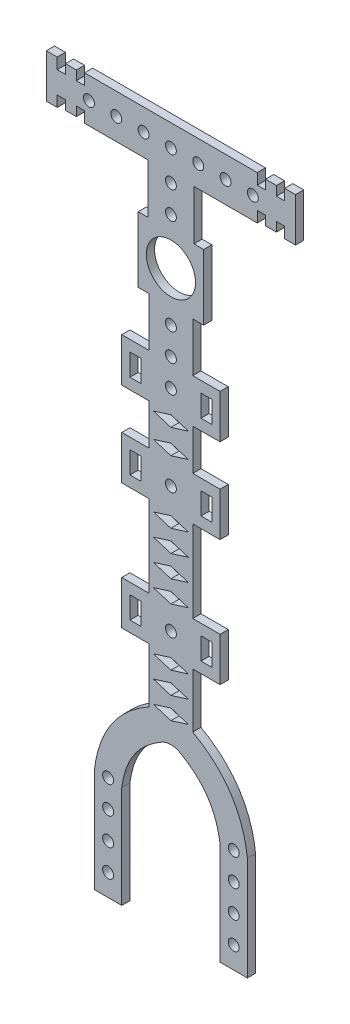
SolidWorks part; units mm, degrees
ref_plane "前视基准面" through (0, 0, 0) normal (0, 0, 1) x (1, 0, 0)
ref_plane "上视基准面" through (0, 0, 0) normal (0, 1, 0) x (1, 0, 0)
ref_plane "右视基准面" through (0, 0, 0) normal (1, 0, 0) x (0, 0, -1)
other "Configuration Table"
sketch "草图1" plane through (0, 0, 0) normal (0, 0, 1) x (1, 0, 0)
  line L0 (0, 13.5) -> (0, 5.7352) construction
  line L1 (0, 0) -> (8.7713, 0) construction
  line L2 (-4.2111, 7) -> (-4.2111, 16.1056)
  line L3 (-6, 7) -> (6, 7)
  line L4 (-6, 7) -> (-6, -5)
  line L5 (-6, -5) -> (6, -5)
  line L6 (6, 7) -> (6, -5)
  line L7 (-6, 7) -> (6, -5) construction
  line L8 (-6, -5) -> (6, 7) construction
  line L9 (-4.2111, 16.1056) -> (-15.8161, 16.1056)
  line L10 (-19.3161, 16.4056) -> (-19.3161, 18.1056)
  line L11 (-20.8161, 24.1056) -> (-22.8161, 24.1056)
  line L12 (20.8161, 16.1056) -> (22.8161, 16.1056)
  line L13 (19.3161, 18.1056) -> (20.8161, 18.1056)
  line L14 (4.2111, 16.1056) -> (4.2111, 7)
  line L15 (-22.8161, 24.1056) -> (-22.8161, 16.1056)
  line L16 (-19.3161, 22.1056) -> (-20.8161, 22.1056)
  line L17 (-20.8161, 22.1056) -> (-20.8161, 24.1056)
  line L18 (-17.3161, 16.4056) -> (-19.3161, 16.4056)
  line L19 (-17.3161, 18.1056) -> (-17.3161, 16.4056)
  line L20 (-15.8161, 18.1056) -> (-17.3161, 18.1056)
  line L21 (20.8161, 18.1056) -> (20.8161, 16.1056)
  line L22 (19.3161, 23.8056) -> (19.3161, 22.1056)
  line L23 (17.3161, 23.8056) -> (19.3161, 23.8056)
  line L24 (17.3161, 22.1056) -> (17.3161, 23.8056)
  line L25 (15.8161, 22.1056) -> (17.3161, 22.1056)
  line L26 (15.8161, 24.1056) -> (15.8161, 22.1056)
  line L27 (-15.8161, 24.1056) -> (15.8161, 24.1056)
  line L28 (-15.8161, 16.1056) -> (-15.8161, 18.1056)
  line L29 (15.8161, 16.1056) -> (15.8161, 18.1056)
  line L30 (15.8161, 16.1056) -> (4.2111, 16.1056)
  line L31 (-25.1648, 20.1056) -> (-15.2017, 20.1056) construction
  line L32 (0, 20.1056) -> (5, 20.1056) construction
  line L33 (0, 20.1056) -> (-5, 20.1056) construction
  line L34 (-4, -14) -> (-4, -5)
  line L35 (-4, -14) -> (-9, -14)
  line L36 (-9, -14) -> (-9, -22)
  line L37 (-9, -22) -> (-4, -22)
  line L38 (-4, -22) -> (-4, -29.5)
  line L39 (-4, -29.5) -> (-9, -29.5)
  line L40 (-9, -29.5) -> (-9, -37.5)
  line L41 (-9, -37.5) -> (-4, -37.5)
  line L42 (-7.5, -31.5) -> (-5.5, -31.5)
  line L43 (-4, -52.5) -> (-9, -52.5)
  line L44 (-9, -52.5) -> (-9, -60.5)
  line L45 (-9, -60.5) -> (-4, -60.5)
  line L46 (-4, -60.5) -> (-4, -70.5)
  line L47 (15.8161, 18.1056) -> (17.3161, 18.1056)
  line L48 (4, -70.5) -> (4, -60.5)
  line L49 (4, -60.5) -> (9, -60.5)
  line L50 (9, -60.5) -> (9, -52.5)
  line L51 (9, -52.5) -> (4, -52.5)
  line L52 (4, -52.5) -> (4, -37.5)
  line L53 (4, -37.5) -> (9, -37.5)
  line L54 (9, -37.5) -> (9, -29.5)
  line L55 (9, -29.5) -> (4, -29.5)
  line L56 (4, -29.5) -> (4, -22)
  line L57 (4, -22) -> (9, -22)
  line L58 (9, -22) -> (9, -14)
  line L59 (9, -14) -> (4, -14)
  line L60 (4, -14) -> (4, -5)
  line L61 (-8.8729, -18) -> (-3.8729, -18) construction
  line L62 (7.5, -20) -> (5.5, -20)
  line L63 (-7.5, -16) -> (-5.5, -16)
  line L64 (-7.5, -16) -> (-7.5, -20)
  line L65 (-7.5, -20) -> (-5.5, -20)
  line L66 (-5.5, -16) -> (-5.5, -20)
  line L67 (-7.5, -16) -> (-5.5, -20) construction
  line L68 (-7.5, -20) -> (-5.5, -16) construction
  line L69 (5.5, -16) -> (5.5, -20)
  line L70 (7.5, -16) -> (5.5, -16)
  line L71 (7.5, -16) -> (7.5, -20)
  line L72 (-4, -37.5) -> (-4, -52.5)
  line L81 (-4, -49) -> (4, -49) construction
  line L90 (-14, -85.5) -> (-14, -104.5)
  line L93 (14, -85.5) -> (14, -104.5)
  line L94 (-9, -85.8077) -> (-9, -104.5)
  line L95 (17.3161, 18.1056) -> (17.3161, 16.4056)
  line L96 (-9, -33.5) -> (9, -33.5) construction
  line L97 (9, -85.8077) -> (9, -104.5)
  line L117 (0, -42.2) -> (-3.2, -43.2)
  line L118 (-3.2, -43.2) -> (0, -44.2)
  line L140 (17.3161, 16.4056) -> (19.3161, 16.4056)
  line L141 (0, -38.2) -> (-3.2, -39.2)
  line L142 (-3.2, -39.2) -> (0, -40.2)
  line L143 (0, -40.2) -> (3.2, -39.2)
  line L144 (3.2, -39.2) -> (0, -38.2)
  line L145 (0, -44.2) -> (3.2, -43.2)
  line L146 (3.2, -43.2) -> (0, -42.2)
  line L147 (0, -46.2) -> (-3.2, -47.2)
  line L148 (-3.2, -47.2) -> (0, -48.2)
  line L149 (0, -48.2) -> (3.2, -47.2)
  line L150 (3.2, -47.2) -> (0, -46.2)
  line L151 (0, -50.2) -> (-3.2, -51.2)
  line L152 (-3.2, -51.2) -> (0, -52.2)
  line L153 (0, -52.2) -> (3.2, -51.2)
  line L154 (3.2, -51.2) -> (0, -50.2)
  line L183 (0, -62.2) -> (-3.2, -63.2) [skipped]
  line L184 (-3.2, -63.2) -> (0, -64.2) [skipped]
  line L185 (0, -64.2) -> (3.2, -63.2) [skipped]
  line L186 (3.2, -63.2) -> (0, -62.2) [skipped]
  line L187 (0, -66.2) -> (-3.2, -67.2) [skipped]
  line L188 (-3.2, -67.2) -> (0, -68.2) [skipped]
  line L189 (0, -68.2) -> (3.2, -67.2) [skipped]
  line L190 (3.2, -67.2) -> (0, -66.2) [skipped]
  line L191 (0, -70.2) -> (-3.2, -71.2) [skipped]
  line L192 (3.2, -71.2) -> (0, -70.2) [skipped]
  line L193 (0, -72.2) -> (3.2, -71.2) [skipped]
  line L194 (-3.2, -71.2) -> (0, -72.2) [skipped]
  line L195 (0, -74.2) -> (-3.2, -75.2) [skipped]
  line L196 (-3.2, -75.2) -> (0, -76.2) [skipped]
  line L197 (0, -76.2) -> (3.2, -75.2) [skipped]
  line L198 (3.2, -75.2) -> (0, -74.2) [skipped]
  line L199 (0, -78.2) -> (-3.2, -79.2) [skipped]
  line L200 (-3.2, -79.2) -> (0, -80.2) [skipped]
  line L201 (0, -80.2) -> (3.2, -79.2) [skipped]
  line L202 (3.2, -79.2) -> (0, -78.2) [skipped]
  line L203 (-15.8161, 24.1056) -> (-15.8161, 22.1056)
  line L206 (0, -60.7) -> (-3.2, -61.7)
  line L207 (-3.2, -61.7) -> (0, -62.7)
  line L208 (0, -62.7) -> (3.2, -61.7)
  line L209 (3.2, -61.7) -> (0, -60.7)
  line L210 (0, -64.7) -> (-3.2, -65.7)
  line L211 (-3.2, -65.7) -> (0, -66.7)
  line L212 (0, -66.7) -> (3.2, -65.7)
  line L213 (3.2, -65.7) -> (0, -64.7)
  line L214 (0, -68.7) -> (-3.2, -69.7)
  line L215 (-3.2, -69.7) -> (0, -70.7)
  line L216 (0, -70.7) -> (3.2, -69.7)
  line L217 (3.2, -69.7) -> (0, -68.7)
  line L224 (0, -26.7) -> (-3.2, -27.7)
  line L225 (-3.2, -27.7) -> (0, -28.7)
  line L226 (0, -28.7) -> (3.2, -27.7)
  line L227 (3.2, -27.7) -> (0, -26.7)
  line L228 (0, -22.2) -> (-3.2, -23.2)
  line L229 (-3.2, -23.2) -> (0, -24.2)
  line L230 (0, -24.2) -> (3.2, -23.2)
  line L231 (3.2, -23.2) -> (0, -22.2)
  line L232 (-9, -56.5) -> (9, -56.5) construction
  line L233 (-15.8161, 22.1056) -> (-17.3161, 22.1056)
  line L234 (-17.3161, 22.1056) -> (-17.3161, 23.8056)
  line L235 (-17.3161, 23.8056) -> (-19.3161, 23.8056)
  line L236 (-19.3161, 23.8056) -> (-19.3161, 22.1056)
  line L237 (-20.8161, 18.1056) -> (-20.8161, 16.1056)
  line L238 (-19.3161, 18.1056) -> (-20.8161, 18.1056)
  line L239 (-20.8161, 16.1056) -> (-22.8161, 16.1056)
  line L240 (20.8161, 22.1056) -> (20.8161, 24.1056)
  line L241 (19.3161, 22.1056) -> (20.8161, 22.1056)
  line L242 (22.8161, 24.1056) -> (22.8161, 16.1056)
  line L243 (20.8161, 24.1056) -> (22.8161, 24.1056)
  line L244 (19.3161, 16.4056) -> (19.3161, 18.1056)
  line L245 (-7.5, -31.5) -> (-7.5, -35.5)
  line L246 (-7.5, -35.5) -> (-5.5, -35.5)
  line L247 (-5.5, -31.5) -> (-5.5, -35.5)
  line L248 (-9, -104.5) -> (-14, -104.5)
  line L249 (-7.5, -31.5) -> (-5.5, -35.5) construction
  line L250 (9, -104.5) -> (14, -104.5)
  line L251 (-11.5, -104.5) -> (-11.5, -87.1492) construction
  line L256 (3.2, -59.2) -> (0, -58.2) [skipped]
  line L257 (0, -60.2) -> (0.9095, -59.9158) [skipped]
  line L258 (0, -58.2) -> (-3.2, -59.2) [skipped]
  line L259 (-3.2, -59.2) -> (-2.24, -59.5) [skipped]
  line L260 (0, -54.2) -> (-3.2, -55.2) [skipped]
  line L261 (-3.2, -55.2) -> (0, -56.2) [skipped]
  line L262 (3.2, -55.2) -> (0, -54.2) [skipped]
  line L263 (0, -56.2) -> (3.2, -55.2) [skipped]
  line L264 (-7.5, -35.5) -> (-5.5, -31.5) construction
  line L265 (-7.5, -54.5) -> (-5.5, -54.5)
  line L266 (-7.5, -54.5) -> (-7.5, -58.5)
  line L267 (-7.5, -58.5) -> (-5.5, -58.5)
  line L268 (-5.5, -54.5) -> (-5.5, -58.5)
  line L269 (-7.5, -54.5) -> (-5.5, -58.5) construction
  line L270 (-7.5, -58.5) -> (-5.5, -54.5) construction
  line L271 (7.5, -35.5) -> (5.5, -31.5) construction
  line L272 (7.5, -31.5) -> (5.5, -35.5) construction
  line L273 (5.5, -31.5) -> (5.5, -35.5)
  line L274 (7.5, -35.5) -> (5.5, -35.5)
  line L275 (7.5, -31.5) -> (7.5, -35.5)
  line L276 (7.5, -31.5) -> (5.5, -31.5)
  line L277 (7.5, -58.5) -> (5.5, -54.5) construction
  line L278 (7.5, -54.5) -> (5.5, -58.5) construction
  line L279 (5.5, -54.5) -> (5.5, -58.5)
  line L280 (7.5, -58.5) -> (5.5, -58.5)
  line L281 (7.5, -54.5) -> (7.5, -58.5)
  line L282 (7.5, -54.5) -> (5.5, -54.5)
  circle A0 centre (0, 1) radius 4.5
  circle A1 centre (0, 9.5405) radius 1
  circle A2 centre (0, 14.5405) radius 1
  circle A3 centre (0, 20.1056) radius 1
  circle A4 centre (5, 20.1056) radius 1
  circle A5 centre (10, 20.1056) radius 1
  circle A6 centre (15, 20.1056) radius 1
  circle A7 centre (-5, 20.1056) radius 1
  circle A8 centre (-10, 20.1056) radius 1
  circle A9 centre (-15, 20.1056) radius 1
  circle A10 centre (0, -18) radius 1
  circle A11 centre (0, -13) radius 1
  circle A12 centre (0, -8) radius 1
  circle A13 centre (0, -33.5) radius 1
  circle A16 centre (-11.5, -100.5) radius 1
  circle A17 centre (-11.5, -95.5) radius 1
  circle A20 centre (11.5, -100.5) radius 1
  circle A21 centre (11.5, -95.5) radius 1
  circle A22 centre (0, -56.5) radius 1
  circle A23 centre (-11.5, -90.5) radius 1
  circle A24 centre (-11.5, -85.5) radius 1
  circle A25 centre (11.5, -85.5) radius 1
  circle A26 centre (11.5, -90.5) radius 1
  spline S0 degree 2 poles (-4, -70.5) (-12.8248, -75.4465) (-14, -85.5) knots 0 0 0 1 1 1
  spline S1 degree 2 poles (4, -70.5) (12.8248, -75.4465) (14, -85.5) knots 0 0 0 1 1 1
  spline S3 degree 2 poles (-1.5553, -74.8616) (-4.1241, -76.3241) (-6.7724, -79.3517) (-8.6016, -82.9141) (-9, -85.8077) knots 0 0 0 0.368595 0.614325 0.98292 0.98292 0.98292
  spline S4 degree 2 poles (-1.5553, -74.8616) (0, -74.1523) (1.5553, -74.8616) knots 0 0 0 1 1 1
  spline S9 degree 2 poles (1.5553, -74.8616) (4.1241, -76.3241) (6.7724, -79.3517) (8.6016, -82.9141) (9, -85.8077) knots 0 0 0 0.368595 0.614325 0.98292 0.98292 0.98292
  point P69 (-6.5, -33.5)
  point P88 (-6.5, -18)
  point P90 (-6.5, -18)
  point P101 (-6.5, -33.5)
  point P106 (-6.5, -56.5)
  point P107 (-6.5, -56.5)
  point P117 (6.5, -33.5)
  point P119 (-14, -85.5)
  point P144 (0, -31.5333)
  point P148 (0, -39.2)
  point P149 (6.5, -56.5)
  point P150 (0, -27.3667)
  point P155 (0, -23.2)
  point P157 (0, -67.2)
  point P158 (0, -43.2)
  point P163 (0, -47.2)
  point P168 (0, -51.2)
  point P174 (0, -75.2)
  point P175 (0, -71.2)
  point P176 (0, -35.7)
  point P182 (0, -61.7)
  point P204 (0, -55.2)
  point P209 (0, -59.2)
  point P214 (0, -79.2)
  point P215 (0, -63.2)
  point P220 (0, -65.7)
  point P225 (0, -69.7)
  point P285 (-22.8161, 20.1056)
  point P294 (22.8161, 20.1056)
  dimension "D1" = 9
  dimension "D17" = 2
  dimension "D19" = 2
  dimension "D43" = 2
  dimension "D45" = 2
  dimension "D47" = 2
  dimension "D2" = 12
  dimension "D3" = 12
  dimension "D6" = 19
  dimension "D7" = 8.4223
  dimension "D8" = 3
  dimension "D9" = 1.5
  dimension "D10" = 31.6322
  dimension "D11" = 2
  dimension "D12" = 4
  dimension "D13" = 15.5
  dimension "D14" = 2
  dimension "D15" = 23
  dimension "D16" = 1.7
  dimension "D21" = 5
  dimension "D23" = 5
  dimension "D25" = 2
  dimension "D27" = 5
  dimension "D28" = 8
  dimension "D31" = 2
  dimension "D32" = 4
  dimension "D33" = 4
  dimension "D34" = 1.5
  dimension "D37" = 10
  dimension "D38" = 10
  dimension "D39" = 15
  dimension "D46" = 4
  dimension "D48" = 2
  dimension "D51" = 6.4
  dimension "D53" = 2
  dimension "D54" = 11
  dimension "D49" = 1.5
  dimension "D50" = 2
  dimension "D18" = 2
  dimension "D20" = 4
  dimension "D22" = 4
  dimension "D44" = 3
extrude "凸台-拉伸1" add sketch "草图1" along normal blind 1.5
